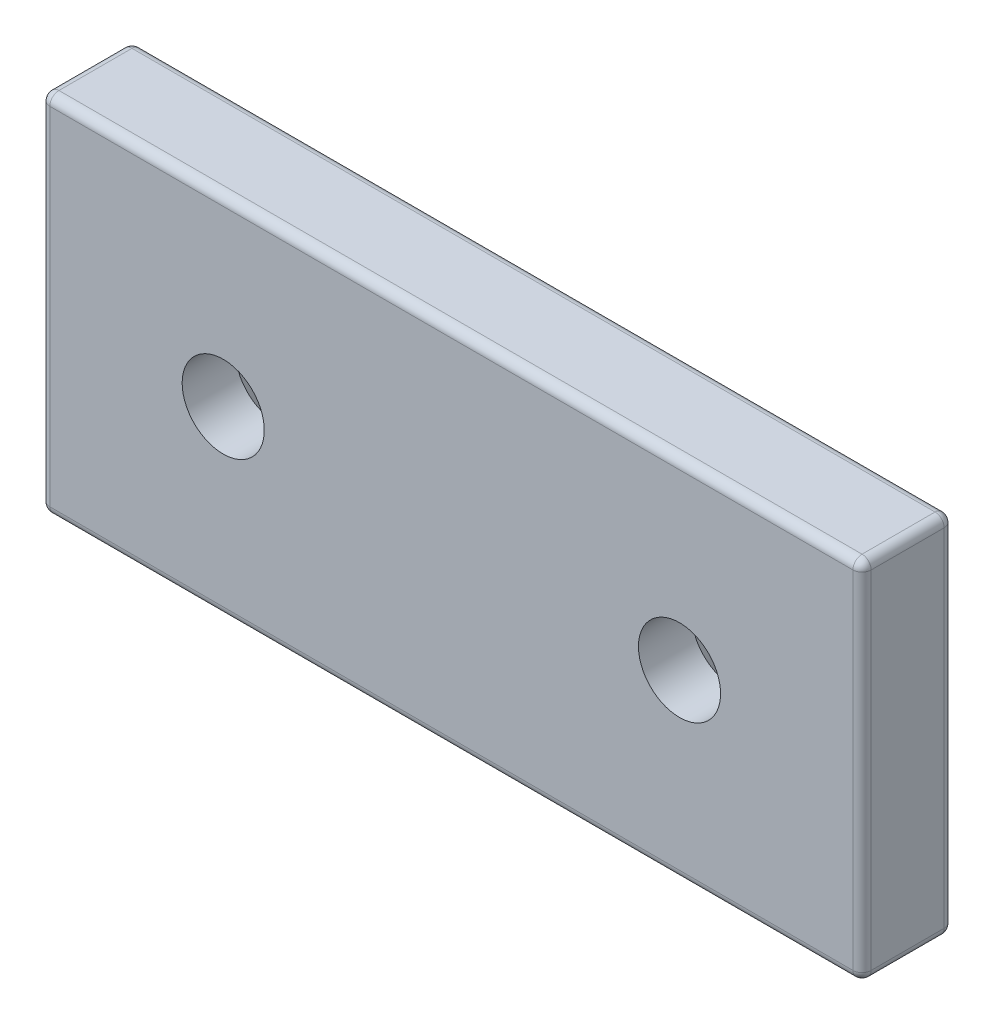
SolidWorks part; units mm, degrees
ref_plane "Front Plane" through (0, 0, 0) normal (0, 0, 1) x (1, 0, 0)
ref_plane "Top Plane" through (0, 0, 0) normal (0, 1, 0) x (1, 0, 0)
ref_plane "Right Plane" through (0, 0, 0) normal (1, 0, 0) x (0, 0, -1)
sketch "Sketch1" plane through (0, 0, 0) normal (0, 0, 1) x (1, 0, 0)
  line L0 (-25, 0) -> (25, 0) construction
  line L1 (-45, -20) -> (45, -20)
  line L2 (-45, -20) -> (-45, 20)
  line L3 (-45, 20) -> (45, 20)
  line L4 (45, -20) -> (45, 20)
  line L5 (-45, -20) -> (45, 20) construction
  line L6 (-45, 20) -> (45, -20) construction
  point P0 (0, 0)
  point P7 (0, 0)
  dimension "D1" = 40
  dimension "D2" = 90
  dimension "D4" = 20
  dimension "D5" = 70
extrude "Boss-Extrude1" add sketch "Sketch1" along normal blind 10
fillet "Fillet1" radius 1 12 edges at (-45, -20, 5) (-45, 20, 5) (45, -20, 5) (45, 20, 5) (0, 20, 0) (-45, 0, 0) (0, -20, 0) (45, 0, 0) (0, -20, 10) (-45, 0, 10) (0, 20, 10) (45, 0, 10)
hole_wizard "CSK for M8 Flat Head Machine Screw1" positions "Sketch2" profile "Sketch3" countersink size "M8" standard "ANSI Metric" end condition through all
sketch "Sketch2" plane through (0, 0, 0) normal (0, 0, -1) x (-1, 0, 0)
  line L0 (25, 0) -> (-25, 0) construction
  point P0 (25, 0)
  point P4 (-25, 0)
  point P8 (23.1058, 0)
sketch "Sketch3" plane through (-25, 0, 0) normal (1, 0, 0) x (0, 1, 0)
  line L0 (0, 0) -> (0, 10)
  line L1 (0, 10) -> (4.5, 10)
  line L2 (4.5, 10) -> (4.5, 4.15)
  line L3 (4.5, 4.15) -> (8.65, 0)
  line L5 (8.65, 0) -> (0, 0)
  line L6 (-4.5, 4.15) -> (-8.65, 0) construction
  line L11 (0, -6.35) -> (0, 107.95) construction
  dimension "Thru Hole Dia." = 9
  dimension "Thru Hole Depth" = 10
  dimension "Near C'Sink Dia." = 17.3
  dimension "Near C'Sink Angle" = 90
